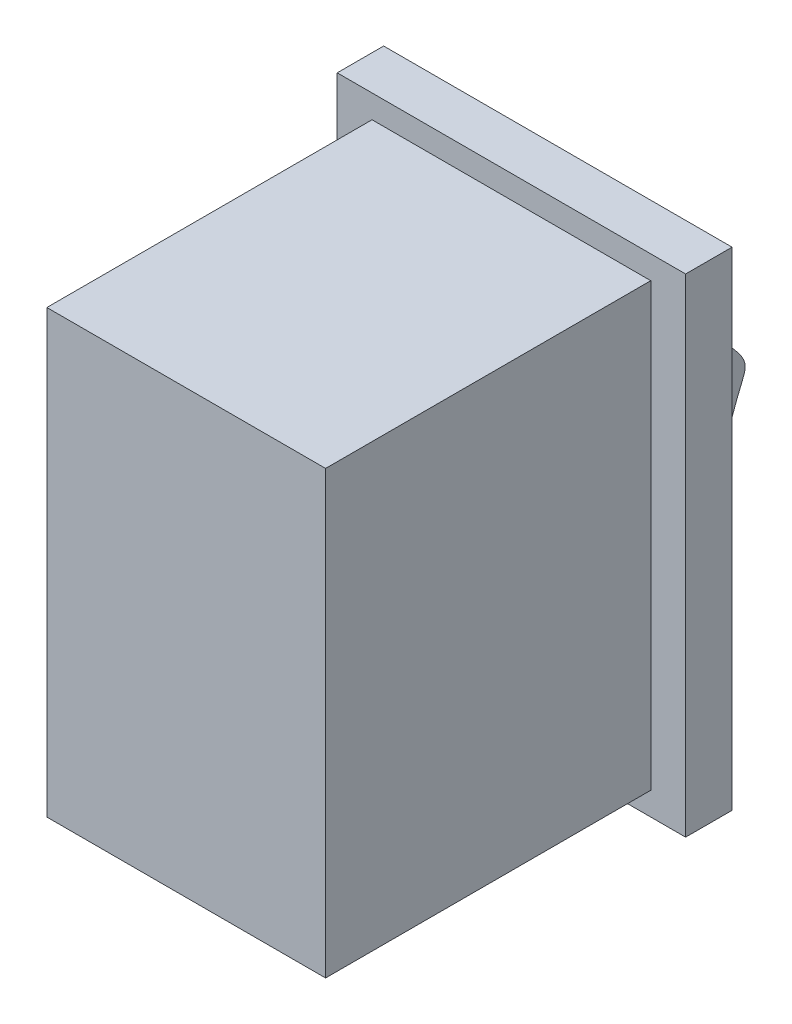
SolidWorks part; units mm, degrees
ref_plane "Front Plane" through (0, 0, 0) normal (0, 0, 1) x (1, 0, 0)
ref_plane "Top Plane" through (0, 0, 0) normal (0, 1, 0) x (1, 0, 0)
ref_plane "Right Plane" through (0, 0, 0) normal (1, 0, 0) x (0, 0, -1)
sketch "Sketch1" plane through (0, 0, 0) normal (0, 0, 1) x (1, 0, 0)
  line L1 (0, 0) -> (12, 0)
  line L2 (0, 0) -> (0, 19)
  line L3 (0, 19) -> (12, 19)
  line L4 (12, 0) -> (12, 19)
  dimension "D1" = 19
  dimension "D2" = 12
extrude "Boss-Extrude1" add sketch "Sketch1" along normal blind 14
sketch "Sketch2" plane through (0, 0, 0) normal (0, 0, 1) x (1, 0, 0)
  line L1 (-1.5, 20) -> (13.5, 20)
  line L2 (-1.5, 20) -> (-1.5, -1)
  line L3 (-1.5, -1) -> (13.5, -1)
  line L4 (13.5, 20) -> (13.5, -1)
  line L5 (-1.5, 20) -> (13.5, -1) construction
  line L6 (-1.5, -1) -> (13.5, 20) construction
  point P0 (6, 9.5)
  dimension "D1" = 15
  dimension "D2" = 21
  dimension "D3" = 6
  dimension "D4" = 9.5
extrude "Boss-Extrude2" add sketch "Sketch2" against normal blind 2
sketch "Sketch3" plane through (0, 0, 0) normal (1, 0, 0) x (0, 0, -1)
  line L0 (2, -1) -> (2, 20) construction
  line L2 (2, 16.5) -> (2, 2.5)
  line L5 (-14, 0) -> (-14, 19) construction
  spline S0 degree 3 poles (2, 2.5) (2, 3.4121) (5.2187, 14.1137) (5.4014, 12.6813) (2, 16.5) knots 0 0 0 0 0.602337 1 1 1 1
  point P1 (0, 0)
  point P9 (-14, 9.5)
  point P11 (0, 0)
  point P12 (5, 12.4499)
  point P14 (0, 0)
  point P15 (0, 0)
  point P16 (0, 0)
extrude "Boss-Extrude3" add sketch "Sketch3" along normal blind 10 from offset 1
